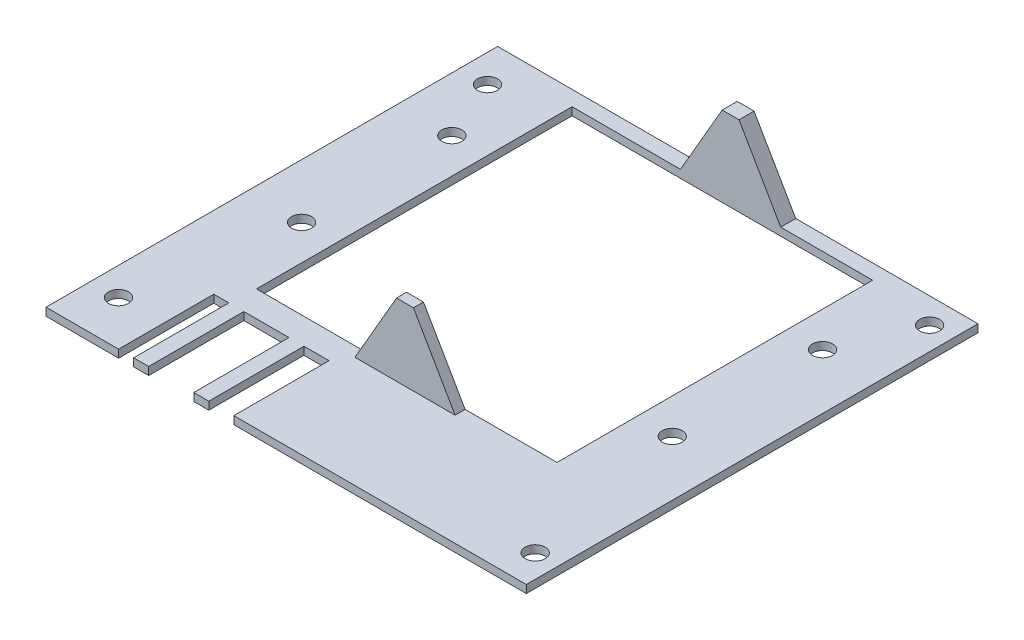
SolidWorks part; units mm, degrees
material "ABS"
ref_plane "Front Plane" through (0, 0, 0) normal (0, 0, 1) x (1, 0, 0)
ref_plane "Top Plane" through (0, 0, 0) normal (0, 1, 0) x (1, 0, 0)
ref_plane "Right Plane" through (0, 0, 0) normal (1, 0, 0) x (0, 0, -1)
sketch "Sketch1" plane through (0, 0, 0) normal (0, 1, 0) x (1, 0, 0)
  line L1 (-32.2441, 108.719) -> (64.6459, 108.719)
  line L2 (-32.2441, 108.719) -> (-32.2441, 18.549)
  line L3 (-32.2441, 18.549) -> (64.6459, 18.549)
  line L4 (64.6459, 108.719) -> (64.6459, 18.549)
  dimension "D1" = 96.89
  dimension "D2" = 90.17
extrude "PCB" add sketch "Sketch1" along normal blind 1.57
sketch "Sketch2" plane through (0, 1.57, 0) normal (0, 1, 0) x (1, 0, 0)
  line L0 (64.6459, 18.549) -> (64.6459, 108.719) construction
  line L1 (-32.2441, 18.549) -> (64.6459, 18.549) construction
  circle A0 centre (59.5659, 24.899) radius 2
  circle A1 centre (-26.1641, 27.439) radius 2
  circle A2 centre (-26.1641, 101.099) radius 2
  circle A3 centre (59.5659, 103.639) radius 2
  dimension "D3" = 4
  dimension "D6" = 4
  dimension "D11" = 4
  dimension "D12" = 4
  dimension "D1" = 5.08
  dimension "D2" = 6.35
  dimension "D4" = 90.81
  dimension "D5" = 8.89
  dimension "D7" = 90.81
  dimension "D8" = 5.08
  dimension "D9" = 85.09
  dimension "D10" = 82.55
extrude "M3 Mounting Holes" cut sketch "Sketch2" against normal blind 1.57
sketch "Sketch3" plane through (0, 1.57, 0) normal (0, 1, 0) x (1, 0, 0)
  line L0 (64.6459, 108.719) -> (-32.2441, 108.719) construction
  line L1 (12.7559, 108.719) -> (22.7559, 108.719)
  line L2 (12.7559, 108.719) -> (12.7559, 106.719)
  line L3 (12.7559, 106.719) -> (22.7559, 106.719)
  line L4 (22.7559, 108.719) -> (22.7559, 106.719)
  line L5 (-32.2441, 108.719) -> (-32.2441, 18.549) construction
  line L7 (12.7559, 42.719) -> (22.7559, 42.719)
  line L8 (12.7559, 42.719) -> (12.7559, 40.719)
  line L9 (12.7559, 40.719) -> (22.7559, 40.719)
  line L10 (22.7559, 42.719) -> (22.7559, 40.719)
  dimension "D1" = 2
  dimension "D2" = 10
  dimension "D3" = 0
  dimension "D4" = 45
  dimension "D5" = 64
  dimension "D6" = 2
  dimension "D7" = 45
extrude "Boss-Extrude1" [suppressed] add sketch "Sketch3" along normal blind 10
sketch "Sketch4" plane through (0, 1.57, 0) normal (0, 1, 0) x (1, 0, 0)
  line L0 (64.6459, 108.719) -> (-32.2441, 108.719) construction
  line L1 (64.6459, 108.719) -> (-32.2441, 108.719) construction
  line L2 (-32.2441, 108.719) -> (-32.2441, 18.549) construction
  line L3 (64.6459, 108.719) -> (-32.2441, 108.719) construction
  circle A0 centre (-20.8941, 88.719) radius 2
  circle A1 centre (53.1059, 88.719) radius 2
  circle A2 centre (-20.8941, 58.719) radius 2
  circle A3 centre (53.1059, 58.719) radius 2
  dimension "D1" = 4
  dimension "D2" = 4
  dimension "D7" = 4
  dimension "D8" = 4
  dimension "D12" = 74
  dimension "D3" = 20
  dimension "D4" = 20
  dimension "D5" = 74
  dimension "D6" = 11.35
  dimension "D9" = 50
  dimension "D10" = 50
  dimension "D11" = 11.35
extrude "Cut-Extrude1" cut sketch "Sketch4" against normal blind 23
ref_plane "Plane1" through (0, 0, -42.719) normal (0, 0, 1) x (1, 0, 0)
sketch "Sketch7" plane through (0, 0, -42.719) normal (0, 0, 1) x (1, 0, 0)
  line L0 (27.7559, 1.57) -> (19.4384, 15.9764)
  line L1 (19.4384, 15.9764) -> (16.0735, 15.9764)
  line L2 (16.0735, 15.9764) -> (7.7559, 1.57)
  line L3 (7.7559, 1.57) -> (27.7559, 1.57)
  line L4 (-32.2441, 1.57) -> (64.6459, 1.57) construction
  dimension "D1" = 60
  dimension "D2" = 60
  dimension "D3" = 0
  dimension "D4" = 3.3649
  dimension "D5" = 20
  dimension "D6" = 5
ref_plane "Plane2" through (0, 0, -108.719) normal (0, 0, 1) x (1, 0, 0)
sketch "Sketch8" plane through (0, 0, -108.719) normal (0, 0, 1) x (1, 0, 0)
  line L0 (27.7559, 1.57) -> (19.4384, 15.9764) construction
  line L1 (19.4384, 15.9764) -> (16.0735, 15.9764) construction
  line L2 (16.0735, 15.9764) -> (7.7559, 1.57) construction
  line L3 (7.7559, 1.57) -> (27.7559, 1.57) construction
  line L4 (27.7559, 1.57) -> (19.4384, 15.9764)
  line L5 (19.4384, 15.9764) -> (16.0735, 15.9764)
  line L6 (16.0735, 15.9764) -> (7.7559, 1.57)
  line L7 (7.7559, 1.57) -> (27.7559, 1.57)
extrude "Boss-Extrude2" add sketch "Sketch7" along normal blind 2
extrude "Boss-Extrude3" add sketch "Sketch8" along normal blind 3
sketch "Sketch9" plane through (0, 1.57, 0) normal (0, 1, 0) x (1, 0, 0)
  line L0 (-32.2441, 18.549) -> (64.6459, 18.549) construction
  line L1 (-14.2441, 18.549) -> (-17.2441, 18.549)
  line L2 (-14.2441, 18.549) -> (-14.2441, 37.549)
  line L3 (-14.2441, 37.549) -> (-17.2441, 37.549)
  line L4 (-17.2441, 18.549) -> (-17.2441, 37.549)
  line L5 (-32.2441, 108.719) -> (-32.2441, 18.549) construction
  line L6 (-11.2441, 18.549) -> (-2.2441, 18.549)
  line L7 (-11.2441, 18.549) -> (-11.2441, 37.549)
  line L8 (-11.2441, 37.549) -> (-2.2441, 37.549)
  line L9 (-2.2441, 18.549) -> (-2.2441, 37.549)
  line L11 (0.7559, 18.549) -> (5.7559, 18.549)
  line L12 (0.7559, 18.549) -> (0.7559, 37.549)
  line L13 (0.7559, 37.549) -> (5.7559, 37.549)
  line L14 (5.7559, 18.549) -> (5.7559, 37.549)
  dimension "D1" = 19
  dimension "D2" = 19
  dimension "D3" = 3
  dimension "D4" = 3
  dimension "D5" = 9
  dimension "D6" = 15
  dimension "D7" = 5
  dimension "D8" = 19
  dimension "D9" = 3
extrude "Cut-Extrude2" cut sketch "Sketch9" against normal through all
sketch "Sketch10" plane through (0, 1.57, 0) normal (0, 1, 0) x (1, 0, 0)
  line L0 (7.7559, 108.719) -> (-32.2441, 108.719) construction
  line L1 (-32.2441, 18.549) -> (-31.7441, 18.549)
  line L2 (-32.2441, 18.549) -> (-32.2441, 108.719)
  line L3 (-32.2441, 108.719) -> (-31.7441, 108.719)
  line L4 (-31.7441, 18.549) -> (-31.7441, 108.719)
  line L5 (64.6459, 108.719) -> (27.7559, 108.719) construction
  line L6 (64.6459, 18.549) -> (64.1459, 18.549)
  line L7 (64.6459, 18.549) -> (64.6459, 108.719)
  line L8 (64.6459, 108.719) -> (64.1459, 108.719)
  line L9 (64.1459, 18.549) -> (64.1459, 108.719)
  dimension "D1" = 0.5
  dimension "D2" = 0.5
extrude "Cut-Extrude3" cut sketch "Sketch10" against normal blind 10
sketch "Sketch11" plane through (0, 1.57, 0) normal (0, 1, 0) x (1, 0, 0)
  line L0 (7.7559, 105.719) -> (27.7559, 105.719) construction
  line L1 (-13.8941, 105.719) -> (46.1059, 105.719)
  line L2 (-13.8941, 105.719) -> (-13.8941, 42.719)
  line L3 (-13.8941, 42.719) -> (46.1059, 42.719)
  line L4 (46.1059, 105.719) -> (46.1059, 42.719)
  dimension "D1" = 60
  dimension "D2" = 63
  dimension "D3" = 0
  dimension "D4" = 7
extrude "Cut-Extrude4" cut sketch "Sketch11" against normal blind 10
